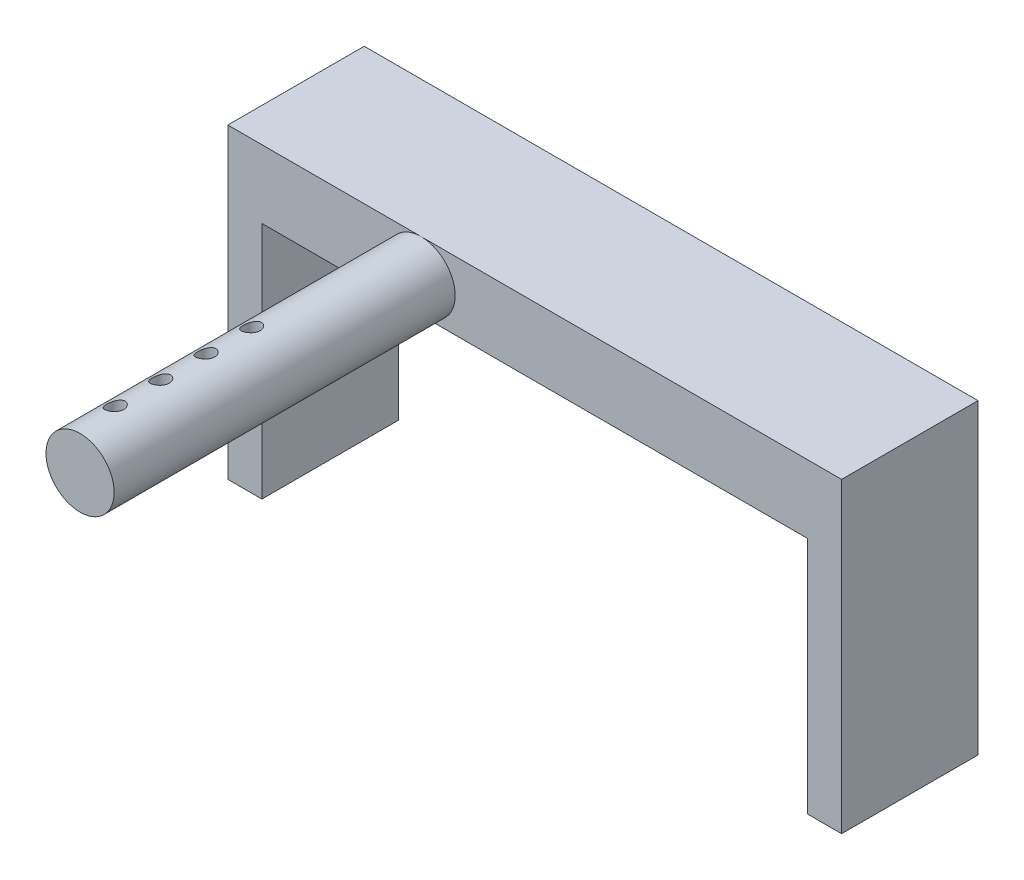
SolidWorks part; units mm, degrees
ref_plane "Front Plane" through (0, 0, 0) normal (0, 0, 1) x (1, 0, 0)
ref_plane "Top Plane" through (0, 0, 0) normal (0, 1, 0) x (1, 0, 0)
ref_plane "Right Plane" through (0, 0, 0) normal (1, 0, 0) x (0, 0, -1)
sketch "Sketch1" plane through (0, 0, 0) normal (0, 0, 1) x (1, 0, 0)
  line L0 (0, 0) -> (0, 27)
  line L1 (0, 27) -> (54, 27)
  line L2 (54, 27) -> (54, 0)
  line L3 (54, 0) -> (51, 0)
  line L4 (51, 0) -> (51, 21)
  line L5 (51, 21) -> (3, 21)
  line L6 (3, 21) -> (3, 0)
  line L7 (3, 0) -> (0, 0)
  point P9 (54, 13.5)
  dimension "D1" = 3
  dimension "D2" = 6
  dimension "D3" = 3
  dimension "D4" = 48
  dimension "D5" = 21
extrude "Boss-Extrude1" add sketch "Sketch1" along normal blind 12
sketch "Sketch2" plane through (0, 0, 12) normal (0, 0, 1) x (1, 0, 0)
  line L0 (54, 27) -> (0, 27) construction
  line L1 (3, 0) -> (3, 21) construction
  circle A0 centre (17, 24) radius 3
  dimension "D1" = 6
  dimension "D2" = 11
extrude "Boss-Extrude2" add sketch "Sketch2" along normal blind 30
sketch "Sketch3" plane through (0, 27, 0) normal (0, 1, 0) x (1, 0, 0)
  line L0 (14, -42) -> (20, -42) construction
  circle A0 centre (16.3465, -38.25) radius 0.75
  circle A1 centre (16.3465, -34.25) radius 0.75
  circle A2 centre (16.3465, -30.25) radius 0.75
  circle A3 centre (16.3465, -26.25) radius 0.75
  dimension "D1" = 1.5
  dimension "D2" = 3
  dimension "D3" = 4
extrude "Cut-Extrude1" cut sketch "Sketch3" against normal up to next
sketch "Sketch4" plane through (0, 0, 0) normal (0, 0, -1) x (-1, 0, 0)
  line L0 (-27, 27) -> (-27, 10.3671) construction
  line L1 (-54, 27) -> (0, 27) construction
  circle A0 centre (-37, 23.8169) radius 1.45
  circle A1 centre (-17, 23.8169) radius 1.45
  point P8 (0, 0)
  dimension "D1" = 2.9
  dimension "D2" = 2.9
  dimension "D3" = 20
extrude "Cut-Extrude2" cut sketch "Sketch4" against normal blind 5
